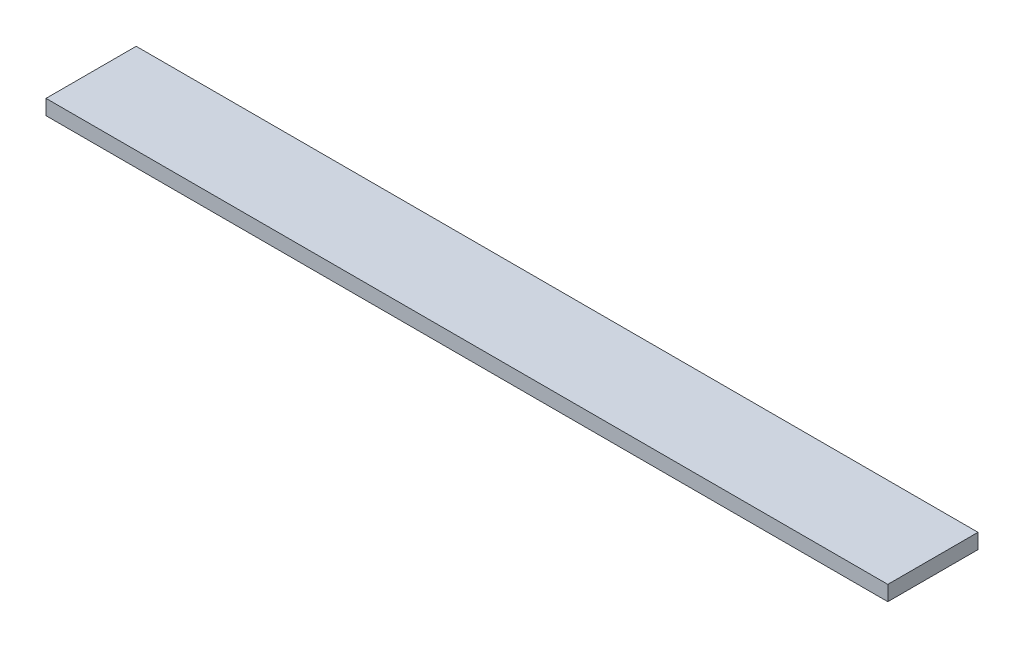
SolidWorks part; units mm, degrees
ref_plane "Front Plane" through (0, 0, 0) normal (0, 0, 1) x (1, 0, 0)
ref_plane "Top Plane" through (0, 0, 0) normal (0, 1, 0) x (1, 0, 0)
ref_plane "Right Plane" through (0, 0, 0) normal (1, 0, 0) x (0, 0, -1)
sketch "Sketch1" plane through (0, 0, 0) normal (0, 1, 0) x (1, 0, 0)
  line L1 (0, 0) -> (711.2, 0)
  line L2 (0, 0) -> (0, 76.2)
  line L3 (0, 76.2) -> (711.2, 76.2)
  line L4 (711.2, 0) -> (711.2, 76.2)
  dimension "D1" = 711.2
  dimension "D2" = 76.2
extrude "Boss-Extrude1" add sketch "Sketch1" along normal blind 12.7
